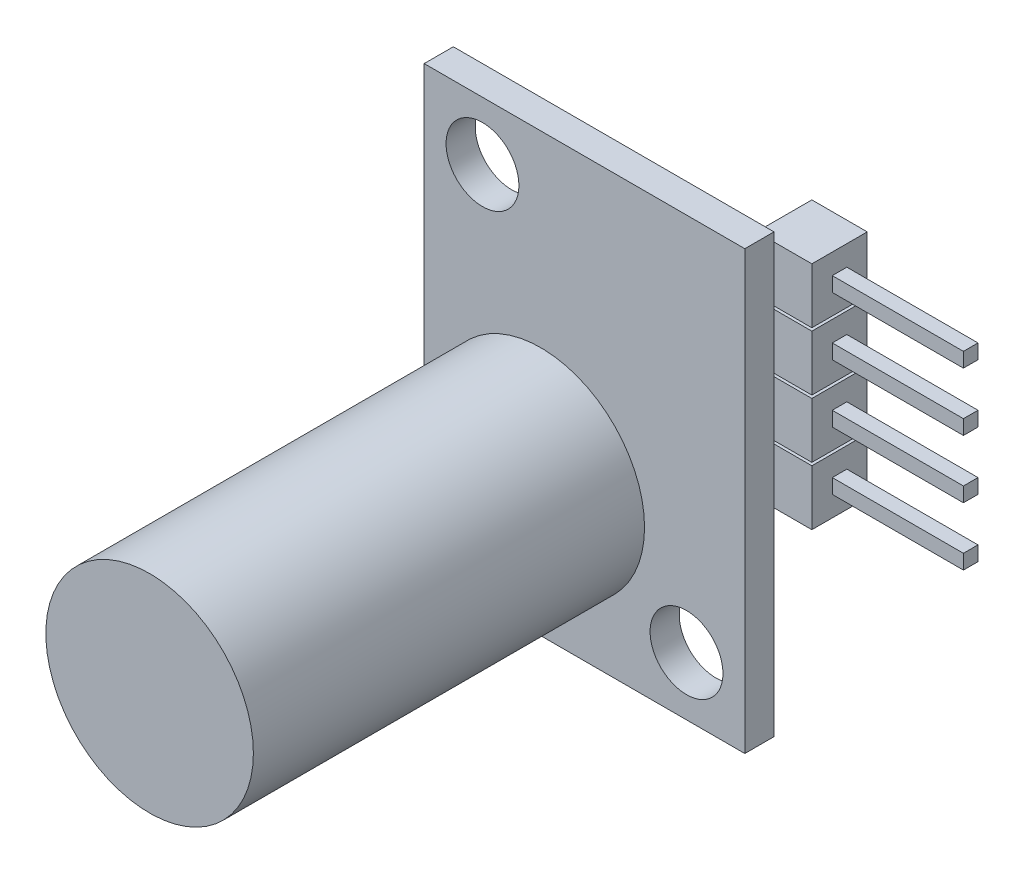
SolidWorks part; units mm, degrees
ref_plane "Front Plane" through (0, 0, 0) normal (0, 0, 1) x (1, 0, 0)
ref_plane "Top Plane" through (0, 0, 0) normal (0, 1, 0) x (1, 0, 0)
ref_plane "Right Plane" through (0, 0, 0) normal (1, 0, 0) x (0, 0, -1)
sketch "Sketch1" plane through (0, 0, 0) normal (0, 0, 1) x (1, 0, 0)
  line L0 (2.54, 16.51) -> (11.43, 16.51) construction
  line L1 (0, 19.05) -> (13.97, 19.05)
  line L2 (0, 19.05) -> (0, 0)
  line L3 (0, 0) -> (13.97, 0)
  line L4 (13.97, 19.05) -> (13.97, 0)
  line L5 (2.54, 2.54) -> (11.43, 2.54) construction
  line L6 (0, 9.525) -> (13.97, 9.525) construction
  line L7 (6.985, 16.51) -> (6.985, 2.54) construction
  circle A0 centre (2.54, 16.51) radius 1.5875
  circle A1 centre (11.43, 2.54) radius 1.5875
  point P13 (6.985, 9.525)
  dimension "D3" = 3.175
  dimension "D1" = 13.97
  dimension "D2" = 19.05
  dimension "D4" = 13.97
  dimension "D5" = 8.89
extrude "Boss-Extrude1" add sketch "Sketch1" along normal blind 1.27
sketch "Sketch2" plane through (0, 0, 1.27) normal (0, 0, 1) x (1, 0, 0)
  line L2 (13.97, 19.05) -> (0, 19.05) construction
  line L3 (13.97, 0) -> (13.97, 19.05) construction
  circle A0 centre (5.08, 6.35) radius 4.5212
  dimension "D1" = 9.0424
  dimension "D3" = 12.7
  dimension "D2" = 8.89
extrude "Boss-Extrude2" add sketch "Sketch2" along normal blind 17.0434
sketch "Sketch3" plane through (0, 0, 0) normal (0, 0, -1) x (-1, 0, 0)
  line L0 (-14.4145, 11.049) -> (-14.4145, 11.176) construction
  line L5 (-15.621, 8.636) -> (-15.621, 11.049)
  line L6 (-15.621, 8.636) -> (-13.208, 8.636)
  line L7 (-13.208, 8.636) -> (-13.208, 11.049)
  line L8 (-15.621, 11.049) -> (-13.208, 11.049)
  line L9 (-15.621, 11.176) -> (-15.621, 13.589)
  line L10 (-15.621, 11.176) -> (-13.208, 11.176)
  line L11 (-13.208, 11.176) -> (-13.208, 13.589)
  line L12 (-15.621, 13.589) -> (-13.208, 13.589)
  line L13 (-15.621, 13.716) -> (-15.621, 16.129)
  line L14 (-15.621, 13.716) -> (-13.208, 13.716)
  line L15 (-13.208, 13.716) -> (-13.208, 16.129)
  line L16 (-15.621, 16.129) -> (-13.208, 16.129)
  line L17 (-15.621, 16.256) -> (-15.621, 18.669)
  line L18 (-15.621, 16.256) -> (-13.208, 16.256)
  line L19 (-13.208, 16.256) -> (-13.208, 18.669)
  line L20 (-15.621, 18.669) -> (-13.208, 18.669)
  line L21 (-14.4145, 13.716) -> (-14.4145, 13.589) construction
  line L23 (-13.97, 0) -> (-13.97, 19.05) construction
  line L24 (-14.4145, 16.256) -> (-14.4145, 16.129) construction
  line L25 (-13.97, 19.05) -> (0, 19.05) construction
  dimension "D1" = 0.127
  dimension "D2" = 0.762
  dimension "D3" = 0.381
  dimension "D4" = 2.413
extrude "Boss-Extrude3" add sketch "Sketch3" along normal blind 2.413
sketch "Sketch4" plane through (15.621, 0, 0) normal (1, 0, 0) x (0, 0, -1)
  line L0 (1.2065, 11.049) -> (1.2065, 8.636) construction
  line L1 (2.413, 11.049) -> (0, 11.049) construction
  line L2 (2.413, 8.636) -> (0, 8.636) construction
  line L5 (0.889, 9.8425) -> (1.524, 9.8425) construction
  line L7 (0.889, 10.16) -> (1.524, 10.16)
  line L8 (0.889, 10.16) -> (0.889, 9.525)
  line L9 (0.889, 9.525) -> (1.524, 9.525)
  line L10 (1.524, 10.16) -> (1.524, 9.525)
  line L134 (0.889, 12.7) -> (0.889, 12.065)
  line L135 (0.889, 12.7) -> (1.524, 12.7)
  line L136 (1.524, 12.7) -> (1.524, 12.065)
  line L137 (0.889, 12.065) -> (1.524, 12.065)
  line L138 (0.889, 15.24) -> (0.889, 14.605)
  line L139 (0.889, 15.24) -> (1.524, 15.24)
  line L140 (1.524, 15.24) -> (1.524, 14.605)
  line L141 (0.889, 14.605) -> (1.524, 14.605)
  line L142 (0.889, 17.78) -> (0.889, 17.145)
  line L143 (0.889, 17.78) -> (1.524, 17.78)
  line L144 (1.524, 17.78) -> (1.524, 17.145)
  line L145 (0.889, 17.145) -> (1.524, 17.145)
  point P8 (1.2065, 9.8425)
  dimension "D1" = 0.635
  dimension "D2" = 4
extrude "Boss-Extrude4" add sketch "Sketch4" along normal blind 5.715
